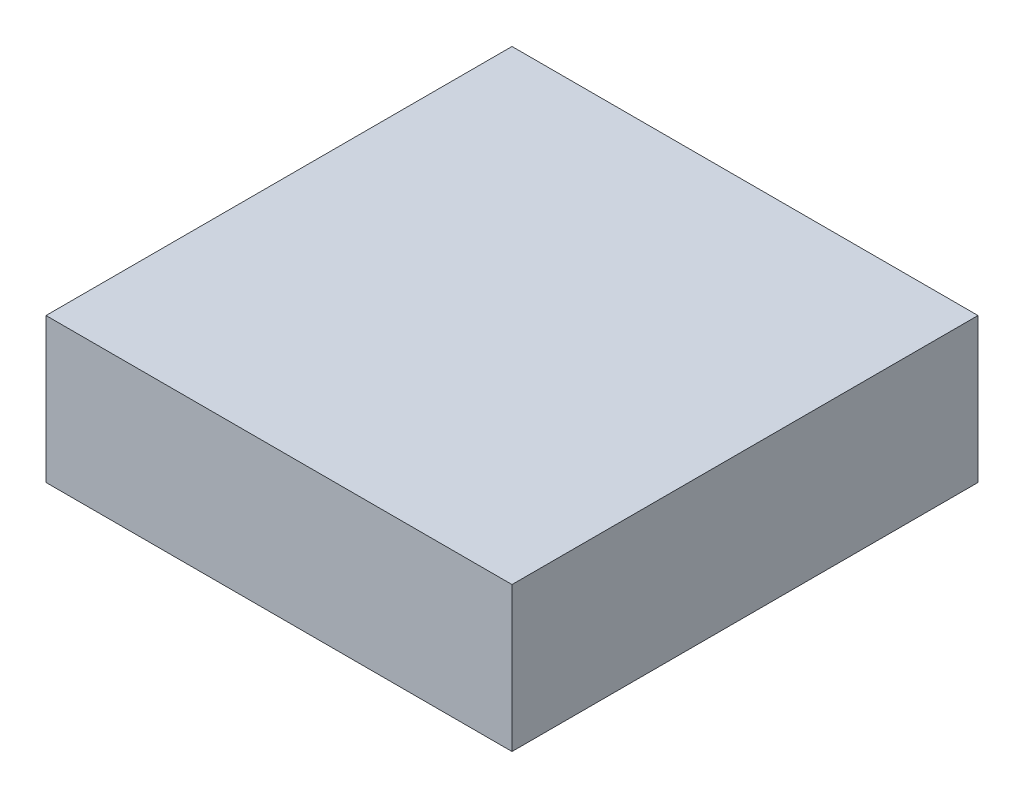
SolidWorks part; units mm, degrees
material "Titanium"
ref_plane "Front Plane" through (0, 0, 0) normal (0, 0, 1) x (1, 0, 0)
ref_plane "Top Plane" through (0, 0, 0) normal (0, 1, 0) x (1, 0, 0)
ref_plane "Right Plane" through (0, 0, 0) normal (1, 0, 0) x (0, 0, -1)
sketch "Sketch1" plane through (0, 0, 0) normal (0, 1, 0) x (1, 0, 0)
  line L1 (-72.5, -72.5) -> (72.5, -72.5)
  line L2 (-72.5, -72.5) -> (-72.5, 72.5)
  line L3 (-72.5, 72.5) -> (72.5, 72.5)
  line L4 (72.5, -72.5) -> (72.5, 72.5)
  line L5 (-72.5, -72.5) -> (72.5, 72.5) construction
  line L6 (-72.5, 72.5) -> (72.5, -72.5) construction
  point P0 (0, 0)
  dimension "D1" = 145
  dimension "D2" = 145
extrude "Boss-Extrude1" add sketch "Sketch1" along normal blind 45
